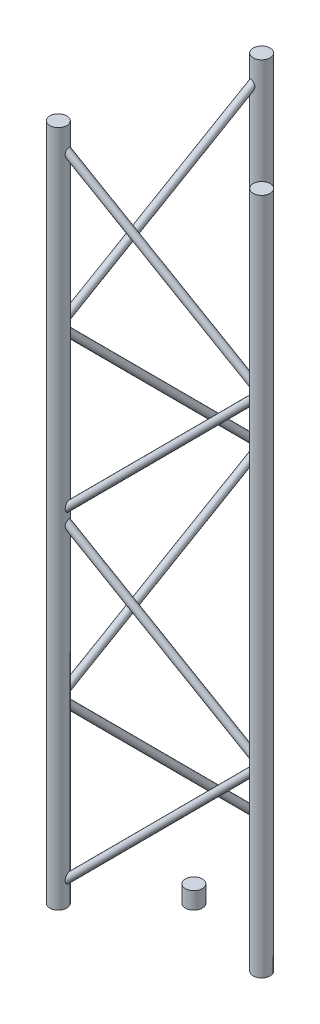
SolidWorks part; units mm, degrees
ref_plane "Front Plane" through (0, 0, 0) normal (0, 0, 1) x (1, 0, 0)
ref_plane "Top Plane" through (0, 0, 0) normal (0, 1, 0) x (1, 0, 0)
ref_plane "Right Plane" through (0, 0, 0) normal (1, 0, 0) x (0, 0, -1)
sketch "Sketch2" plane through (0, 0, 0) normal (0, 1, 0) x (1, 0, 0)
  circle A0 centre (0, 0) radius 25
  dimension "D1" = 50
extrude "Boss-Extrude2" add sketch "Sketch2" along normal blind 50 separate body
sketch "Sketch1" plane through (0, 0, 0) normal (0, 1, 0) x (1, 0, 0)
  line L1 (-200, -115.4701) -> (200, -115.4701) construction
  line L2 (200, -115.4701) -> (0, 230.9401) construction
  line L3 (0, 230.9401) -> (-200, -115.4701) construction
  circle A0 centre (-200, -200) radius 25
  circle A1 centre (0, 0) radius 115.4701 construction
  point P2 (0, 230.9401)
  point P4 (-200, -200)
  dimension "D1" = 50
  dimension "D2" = 200
  dimension "D3" = 200
  dimension "D4" = 400
extrude "Boss-Extrude1" add sketch "Sketch1" along normal blind 2000
pattern_circular "CirPattern1" count 3 over 360 about axis through (0, 0, 0) along (0, 1, 0) of bodies 101
ref_plane "Plane1" through (100, 0, -100) normal (-0.7071, 0, 0.7071) x (0.7071, 0, 0.7071)
sketch "Sketch3" plane through (100, 0, -100) normal (-0.7071, 0, 0.7071) x (0.7071, 0, 0.7071)
  line L0 (244.949, 50) -> (-244.949, 525)
  line L1 (-244.949, 525) -> (244.949, 1000)
  line L2 (244.949, 1000) -> (-244.949, 1475)
  line L10 (-244.949, 1475) -> (244.949, 1950)
  line L11 (244.949, 2000) -> (244.949, 0) construction
  line L12 (269.949, 2000) -> (219.949, 2000) construction
  line L13 (219.949, 0) -> (269.949, 0) construction
  line L14 (-244.949, 2000) -> (-244.949, 0) construction
  dimension "D1" = 50
  dimension "D2" = 50
other "Pipe 21.3 X 2.3(3)"
ref_plane "Plane2" through (-73.2051, 1475, -273.2051) normal (0.5077, 0.6961, 0.5077) x (-0.4922, 0.7179, -0.4922)
sketch "Sketch16" plane through (-73.2051, 1475, -273.2051) normal (0.5077, 0.6961, 0.5077) x (-0.4922, 0.7179, -0.4922)
  circle A0 centre (0, 0) radius 8.35
  circle A1 centre (0, 0) radius 10.65
  point P3 (0, 0)
  dimension "In_dia" = 16.7
  dimension "Out_dia" = 21.3
pattern_circular "CirPattern2" count 3 over 360 about axis through (0, 0, 0) along (0, 1, 0) of bodies 165 164 163 162
